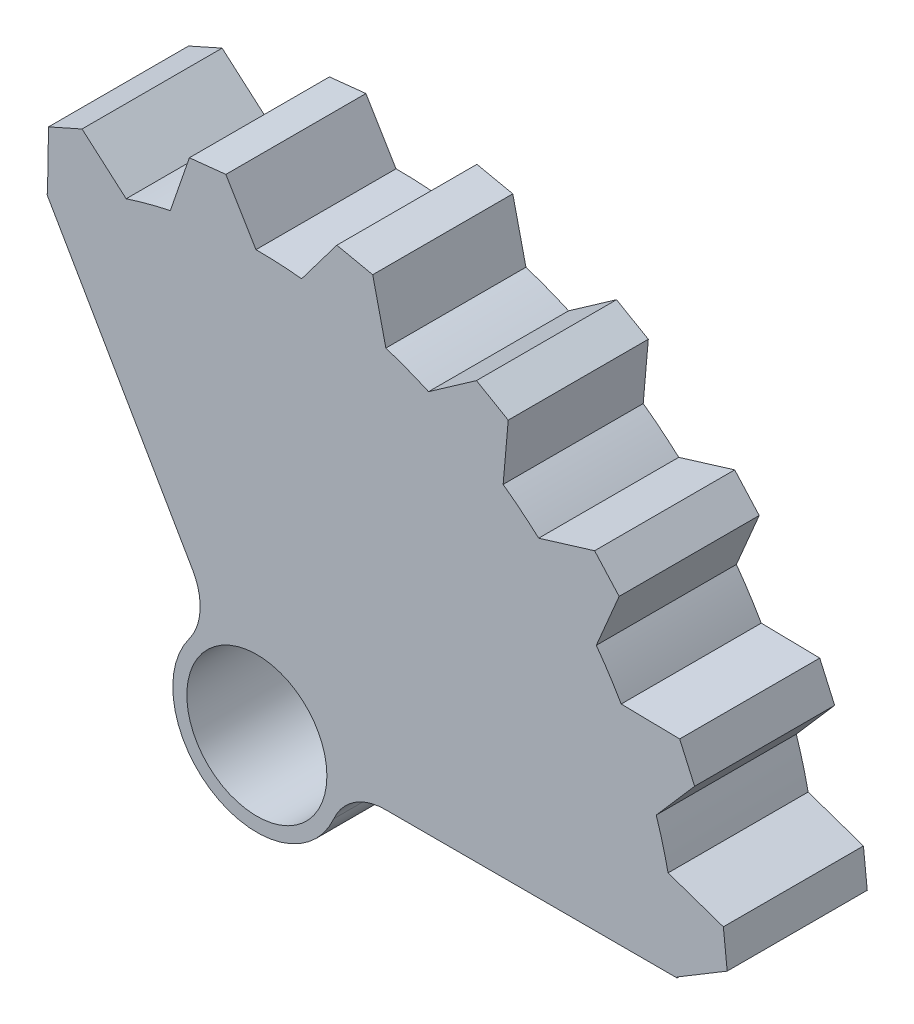
SolidWorks part; units mm, degrees
ref_plane "Front Plane" through (0, 0, 0) normal (0, 0, 1) x (1, 0, 0)
ref_plane "Top Plane" through (0, 0, 0) normal (0, 1, 0) x (1, 0, 0)
ref_plane "Right Plane" through (0, 0, 0) normal (1, 0, 0) x (0, 0, -1)
sketch "Sketch1" plane through (0, 0, 0) normal (0, 0, 1) x (1, 0, 0)
  line L0 (3, 0) -> (15, 0)
  line L1 (-1.5, 2.5981) -> (-7.5, 12.9904)
  line L2 (10.1435, 11.1517) -> (12.0561, 11.7364)
  line L3 (12.0561, 11.7364) -> (12.9323, 10.7633)
  line L4 (12.1509, 8.9222) -> (12.9323, 10.7633)
  line L5 (6.201, 13.7404) -> (7.8393, 14.8875)
  line L6 (8.799, 12.2404) -> (8.9733, 14.2328)
  line L7 (7.8393, 14.8875) -> (8.9733, 14.2328)
  line L8 (8.799, 12.2404) -> (8.7914, 12.1536)
  line L9 (6.201, 13.7404) -> (6.1296, 13.6904)
  line L10 (10.1435, 11.1517) -> (10.0602, 11.1262)
  line L11 (12.1509, 8.9222) -> (12.1168, 8.8421)
  line L12 (13.0931, 7.4714) -> (15.0928, 7.4365)
  line L13 (15.0928, 7.4365) -> (15.6254, 6.2402)
  line L14 (14.3133, 4.7307) -> (15.6254, 6.2402)
  line L15 (13.0931, 7.4714) -> (13.006, 7.4729)
  line L16 (14.3133, 4.7307) -> (14.2561, 4.665)
  line L17 (14.761, 3.0597) -> (16.6521, 2.4086)
  line L18 (16.6521, 2.4086) -> (16.789, 1.1062)
  line L19 (15.0746, 0.0761) -> (16.789, 1.1062)
  line L20 (14.761, 3.0597) -> (14.6787, 3.0881)
  line L21 (15.0746, 0.0761) -> (15, 0.0313)
  line L22 (0, 0) -> (4.7707, 8.2631) construction
  line L87 (-7.4714, 13.0931) -> (-7.4365, 15.0928)
  line L88 (-7.4365, 15.0928) -> (-6.2402, 15.6254)
  line L89 (-4.7307, 14.3133) -> (-6.2402, 15.6254)
  line L90 (-7.4714, 13.0931) -> (-7.4729, 13.006)
  line L91 (-4.7307, 14.3133) -> (-4.665, 14.2561)
  line L92 (-3.0597, 14.761) -> (-2.4086, 16.6521)
  line L93 (-2.4086, 16.6521) -> (-1.1062, 16.789)
  line L94 (-0.0761, 15.0746) -> (-1.1062, 16.789)
  line L95 (-3.0597, 14.761) -> (-3.0881, 14.6787)
  line L96 (-0.0761, 15.0746) -> (-0.0313, 15)
  line L97 (1.6515, 14.9841) -> (2.8551, 16.5814)
  line L98 (2.8551, 16.5814) -> (4.136, 16.3091)
  line L99 (4.5859, 14.3603) -> (4.136, 16.3091)
  line L100 (1.6515, 14.9841) -> (1.599, 14.9145)
  line L101 (4.5859, 14.3603) -> (4.6055, 14.2755)
  line L102 (14.3603, -4.5859) -> (16.3091, -4.136) [skipped]
  line L103 (16.5814, -2.8551) -> (16.3091, -4.136) [skipped]
  line L104 (14.9841, -1.6515) -> (16.5814, -2.8551) [skipped]
  line L105 (-12.1509, -8.9222) -> (-12.9323, -10.7633) [skipped]
  line L106 (-10.1435, -11.1517) -> (-10.0602, -11.1262) [skipped]
  line L107 (-12.1509, -8.9222) -> (-12.1168, -8.8421) [skipped]
  line L108 (-13.0931, -7.4714) -> (-15.0928, -7.4365) [skipped]
  line L109 (-15.0928, -7.4365) -> (-15.6254, -6.2402) [skipped]
  line L110 (-14.3133, -4.7307) -> (-15.6254, -6.2402) [skipped]
  line L111 (-13.0931, -7.4714) -> (-13.006, -7.4729) [skipped]
  line L112 (-14.3133, -4.7307) -> (-14.2561, -4.665) [skipped]
  line L113 (-14.761, -3.0597) -> (-16.6521, -2.4086) [skipped]
  line L114 (-16.6521, -2.4086) -> (-16.789, -1.1062) [skipped]
  line L115 (-15.0746, -0.0761) -> (-16.789, -1.1062) [skipped]
  line L116 (-14.761, -3.0597) -> (-14.6787, -3.0881) [skipped]
  line L117 (-15.0746, -0.0761) -> (-15, -0.0313) [skipped]
  line L118 (-14.9841, 1.6515) -> (-16.5814, 2.8551) [skipped]
  line L119 (-16.5814, 2.8551) -> (-16.3091, 4.136) [skipped]
  line L120 (-14.3603, 4.5859) -> (-16.3091, 4.136) [skipped]
  line L121 (-14.9841, 1.6515) -> (-14.9145, 1.599) [skipped]
  line L122 (-14.3603, 4.5859) -> (-14.2755, 4.6055) [skipped]
  line L123 (-13.7404, 6.201) -> (-14.8875, 7.8393) [skipped]
  line L124 (-14.8875, 7.8393) -> (-14.2328, 8.9733) [skipped]
  line L125 (-12.2404, 8.799) -> (-14.2328, 8.9733) [skipped]
  line L126 (-13.7404, 6.201) -> (-13.6904, 6.1296) [skipped]
  line L127 (-12.2404, 8.799) -> (-12.1536, 8.7914) [skipped]
  line L128 (13.7404, -6.201) -> (14.8875, -7.8393) [skipped]
  line L129 (14.8875, -7.8393) -> (14.2328, -8.9733) [skipped]
  line L130 (12.2404, -8.799) -> (14.2328, -8.9733) [skipped]
  line L131 (13.7404, -6.201) -> (13.6904, -6.1296) [skipped]
  line L132 (12.2404, -8.799) -> (12.1536, -8.7914) [skipped]
  line L133 (11.1517, -10.1435) -> (11.7364, -12.0561) [skipped]
  line L134 (11.7364, -12.0561) -> (10.7633, -12.9323) [skipped]
  line L135 (8.9222, -12.1509) -> (10.7633, -12.9323) [skipped]
  line L136 (11.1517, -10.1435) -> (11.1262, -10.0602) [skipped]
  line L137 (8.9222, -12.1509) -> (8.8421, -12.1168) [skipped]
  line L138 (7.4714, -13.0931) -> (7.4365, -15.0928) [skipped]
  line L139 (7.4365, -15.0928) -> (6.2402, -15.6254) [skipped]
  line L140 (4.7307, -14.3133) -> (6.2402, -15.6254) [skipped]
  line L141 (7.4714, -13.0931) -> (7.4729, -13.006) [skipped]
  line L142 (4.7307, -14.3133) -> (4.665, -14.2561) [skipped]
  line L143 (3.0597, -14.761) -> (2.4086, -16.6521) [skipped]
  line L144 (2.4086, -16.6521) -> (1.1062, -16.789) [skipped]
  line L145 (0.0761, -15.0746) -> (1.1062, -16.789) [skipped]
  line L146 (3.0597, -14.761) -> (3.0881, -14.6787) [skipped]
  line L147 (0.0761, -15.0746) -> (0.0313, -15) [skipped]
  line L148 (-1.6515, -14.9841) -> (-2.8551, -16.5814) [skipped]
  line L149 (-2.8551, -16.5814) -> (-4.136, -16.3091) [skipped]
  line L150 (-4.5859, -14.3603) -> (-4.136, -16.3091) [skipped]
  line L151 (-1.6515, -14.9841) -> (-1.599, -14.9145) [skipped]
  line L152 (-4.5859, -14.3603) -> (-4.6055, -14.2755) [skipped]
  line L153 (-6.201, -13.7404) -> (-7.8393, -14.8875) [skipped]
  line L154 (-7.8393, -14.8875) -> (-8.9733, -14.2328) [skipped]
  line L155 (-8.799, -12.2404) -> (-8.9733, -14.2328) [skipped]
  line L156 (-6.201, -13.7404) -> (-6.1296, -13.6904) [skipped]
  line L157 (-8.799, -12.2404) -> (-8.7914, -12.1536) [skipped]
  line L158 (-10.1435, -11.1517) -> (-12.0561, -11.7364) [skipped]
  line L159 (-12.0561, -11.7364) -> (-12.9323, -10.7633) [skipped]
  line L160 (-11.1517, 10.1435) -> (-11.7364, 12.0561) [skipped]
  line L161 (-11.7364, 12.0561) -> (-10.7633, 12.9323) [skipped]
  line L162 (-8.9222, 12.1509) -> (-10.7633, 12.9323) [skipped]
  line L163 (-11.1517, 10.1435) -> (-11.1262, 10.0602) [skipped]
  line L164 (-8.9222, 12.1509) -> (-8.8421, 12.1168) [skipped]
  line L165 (14.9841, -1.6515) -> (14.9145, -1.599) [skipped]
  line L166 (14.3603, -4.5859) -> (14.2755, -4.6055) [skipped]
  arc A0 (15, 0) -> (15, 0.0313) centre (0, 0) ccw
  arc A1 (6.1296, 13.6904) -> (4.6055, 14.2755) centre (0, 0) ccw
  arc A2 (-7.4729, 13.006) -> (-7.5, 12.9904) centre (0, 0) ccw
  arc A3 (-3.0881, 14.6787) -> (-4.665, 14.2561) centre (0, 0) ccw
  arc A4 (1.599, 14.9145) -> (-0.0313, 15) centre (0, 0) ccw
  arc A5 (10.0602, 11.1262) -> (8.7914, 12.1536) centre (0, 0) ccw
  arc A6 (13.006, 7.4729) -> (12.1168, 8.8421) centre (0, 0) ccw
  arc A7 (14.6787, 3.0881) -> (14.2561, 4.665) centre (0, 0) ccw
  circle A8 centre (0, 0) radius 2.5
  circle A9 centre (0, 0) radius 3
  point P126 (0, 0)
  dimension "D1" = 20
  dimension "D3" = 60
  dimension "D4" = 6
  dimension "D2" = 120
  dimension "D6" = 2
extrude "Boss-Extrude1" add sketch "Sketch1" along normal blind 5
fillet "Fillet1" radius 2 1 edges at (-1.5, 2.5981, 2.5)
fillet "Fillet2" radius 2 1 edges at (3, 0, 2.5)
